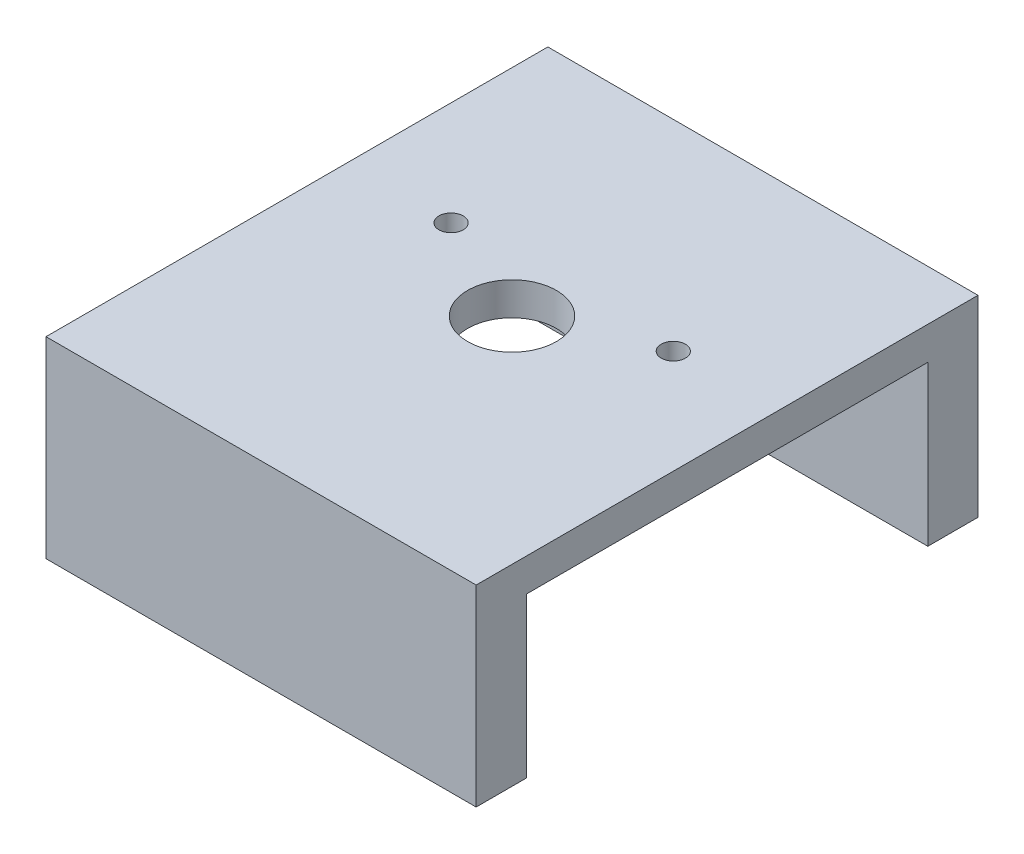
SolidWorks part; units mm, degrees
ref_plane "Front Plane" through (0, 0, 0) normal (0, 0, 1) x (1, 0, 0)
ref_plane "Top Plane" through (0, 0, 0) normal (0, 1, 0) x (1, 0, 0)
ref_plane "Right Plane" through (0, 0, 0) normal (1, 0, 0) x (0, 0, -1)
sketch "Sketch2" plane through (0, 0, 0) normal (0, 1, 0) x (1, 0, 0)
  line L1 (0, 0) -> (60, 0)
  line L2 (0, 0) -> (0, 70)
  line L3 (0, 70) -> (60, 70)
  line L4 (60, 0) -> (60, 70)
  dimension "D1" = 70
  dimension "D2" = 60
extrude "Boss-Extrude1" add sketch "Sketch2" along normal blind 4.5974
sketch "Sketch4" plane through (0, 4.5974, 0) normal (0, 1, 0) x (1, 0, 0)
  line L0 (30, 70) -> (30, 0) construction
  line L1 (60, 70) -> (0, 70) construction
  line L2 (0, 0) -> (60, 0) construction
  line L3 (14.5, 42) -> (45.5, 42) construction
  line L4 (45.5, 42) -> (30, 42) construction
  circle A0 centre (30, 35) radius 6.1905
  circle A1 centre (45.5, 42) radius 1.6905
  circle A2 centre (14.5, 42) radius 1.6905
  dimension "D1" = 12.381
  dimension "D4" = 3.381
  dimension "D2" = 7
  dimension "D3" = 31
extrude "Cut-Extrude1" cut sketch "Sketch4" against normal through all
sketch "Sketch5" plane through (0, 0, -70) normal (0, 0, -1) x (-1, 0, 0)
  line L0 (-60, 0) -> (0, 0)
  line L1 (0, 0) -> (0, -22.225)
  line L3 (0, -22.225) -> (-60, -22.225)
  line L4 (-60, -22.225) -> (-60, 0)
  dimension "D1" = 22.225
extrude "Boss-Extrude2" add sketch "Sketch5" against normal blind 7
ref_plane "Plane1" through (0, 0, -35) normal (0, 0, -1) x (-1, 0, 0)
hole_wizard "#6-32 Tapped Hole1" positions "Sketch7" profile "Sketch8" tap size "#6-32" standard "ANSI Inch"
sketch "Sketch7" plane through (0, -22.225, 0) normal (0, -1, 0) x (-1, 0, 0)
  line L0 (-60, 66.5) -> (-53.65, 66.3249) construction
  line L1 (-60, 63) -> (-60, 70) construction
  line L3 (0, 66.5) -> (-6.351, 66.3681) construction
  line L4 (0, 63) -> (0, 70) construction
  point P0 (-6.351, 66.3681)
  point P2 (-53.65, 66.3249)
  dimension "D1" = 6.35
sketch "Sketch8" plane through (6.351, -22.225, -66.3681) normal (1, 0, 0) x (0, 0, -1)
  line L0 (0, 0) -> (0, 26.2127)
  line L1 (0, 26.2127) -> (1.3525, 25.4)
  line L2 (1.3525, 25.4) -> (1.3525, 0)
  line L5 (1.3525, 0) -> (0, 0)
  line L10 (0, 26.2127) -> (-1.3526, 25.4) construction
  line L11 (0, -6.35) -> (0, 107.95) construction
  dimension "Tap Drill Dia." = 2.7051
  dimension "Tap Drill Depth" = 25.4
  dimension "Drill Angle" = 118
mirror "Mirror1" about plane through (0, 0, -35) normal (0, 0, -1) of "#6-32 Tapped Hole1", "Boss-Extrude2"
